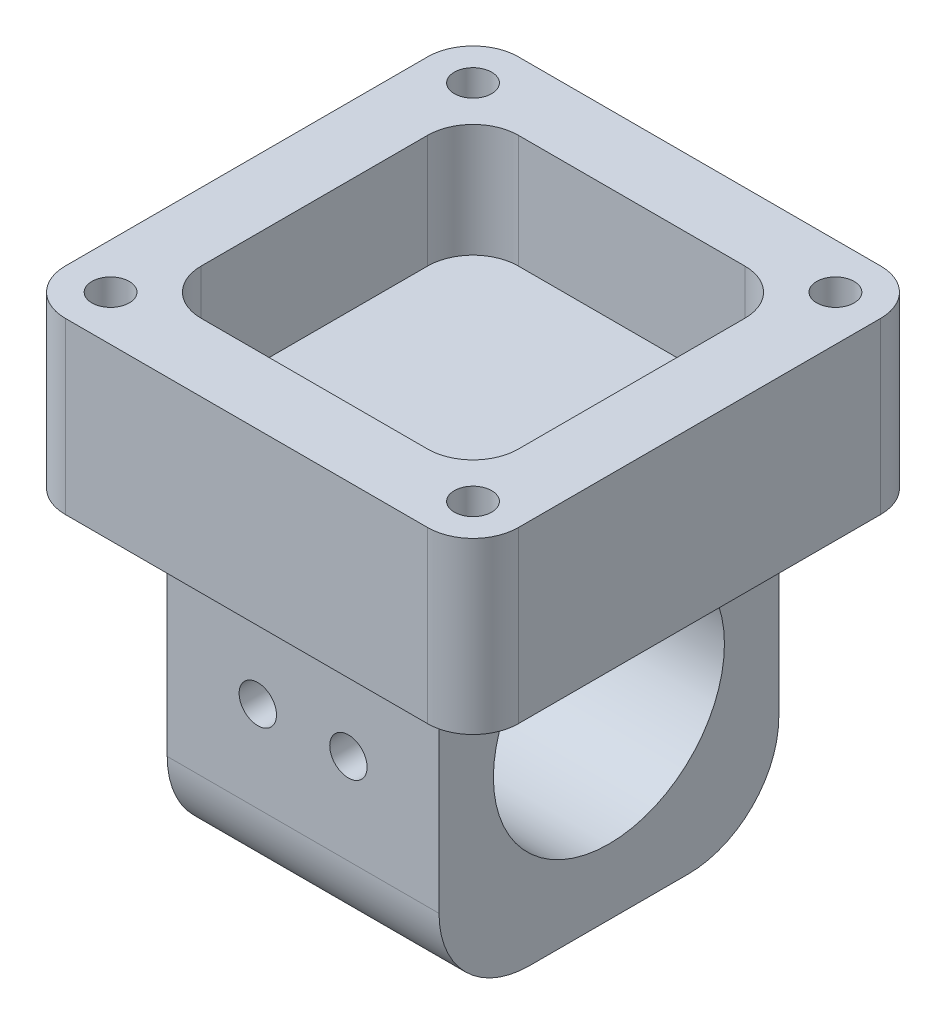
SolidWorks part; units mm, degrees
ref_plane "Front Plane" through (0, 0, 0) normal (0, 0, 1) x (1, 0, 0)
ref_plane "Top Plane" through (0, 0, 0) normal (0, 1, 0) x (1, 0, 0)
ref_plane "Right Plane" through (0, 0, 0) normal (1, 0, 0) x (0, 0, -1)
sketch "Sketch1" plane through (0, 0, 0) normal (0, 1, 0) x (1, 0, 0)
  line L1 (-12, -15) -> (12, -15)
  line L2 (-12, -15) -> (-12, 15)
  line L3 (-12, 15) -> (12, 15)
  line L4 (12, -15) -> (12, 15)
  line L5 (-12, -15) -> (12, 15) construction
  line L6 (-12, 15) -> (12, -15) construction
  point P0 (0, 0)
  dimension "D1" = 30
  dimension "D2" = 24
extrude "Boss-Extrude1" add sketch "Sketch1" along normal mid plane 22
sketch "Sketch2" plane through (0, 0, -15) normal (0, 0, -1) x (-1, 0, 0)
  line L0 (0, 0) -> (0, -5.5397) construction
  circle A0 centre (4, 0) radius 1.65
  circle A2 centre (-4, 0) radius 1.65
  dimension "D1" = 3.3
  dimension "D2" = 4
extrude "Cut-Extrude1" cut sketch "Sketch2" against normal up to surface (30 mm away) up to face at (0, 0, 15)
sketch "Sketch3" plane through (-12, 0, 0) normal (-1, 0, 0) x (0, 0, 1)
  circle A0 centre (0, 0) radius 10.2
  dimension "D1" = 20.4
extrude "Cut-Extrude2" cut sketch "Sketch3" against normal up to surface (24 mm away) up to face at (12, 0, 0)
ref_plane "Plane1" through (0, 16, 0) normal (0, 1, 0) x (1, 0, 0)
sketch "Sketch5" plane through (0, 16, 0) normal (0, 1, 0) x (1, 0, 0)
  line L1 (20, 20) -> (-20, 20)
  line L2 (20, 20) -> (20, -20)
  line L3 (20, -20) -> (-20, -20)
  line L4 (-20, 20) -> (-20, -20)
  line L5 (20, 20) -> (-20, -20) construction
  line L6 (20, -20) -> (-20, 20) construction
  point P0 (0, 0)
  dimension "D1" = 40
extrude "Boss-Extrude3" add sketch "Sketch5" against normal up to surface (5 mm away) up to face at (0, 11, 0)
sketch "Sketch8" plane through (0, 16, 0) normal (0, 1, 0) x (1, 0, 0)
  line L1 (20, 20) -> (-20, 20)
  line L2 (20, 20) -> (20, -20)
  line L3 (20, -20) -> (-20, -20)
  line L4 (-20, 20) -> (-20, -20)
  line L5 (20, 20) -> (-20, -20) construction
  line L6 (20, -20) -> (-20, 20) construction
  line L7 (14, 14) -> (-14, 14)
  line L8 (14, 14) -> (14, -14)
  line L9 (14, -14) -> (-14, -14)
  line L10 (-14, 14) -> (-14, -14)
  line L11 (14, 14) -> (-14, -14) construction
  line L12 (14, -14) -> (-14, 14) construction
  point P0 (0, 0)
  point P7 (0, 0)
  line M9 (-20, 20) -> (-20, -20)
  line M10 (-20, -20) -> (20, -20)
  line M11 (20, -20) -> (20, 20)
  line M12 (20, 20) -> (-20, 20)
  dimension "D1" = 6
extrude "Boss-Extrude4" add sketch "Sketch8" along normal blind 10 contours L10 L7 L8 L9 M12 M9 M10 M11
sketch "Sketch9" plane through (0, 26, 0) normal (0, 1, 0) x (1, 0, 0)
  line L0 (0, 0) -> (-8.5639, 0) construction
  line L1 (0, 0) -> (0, -7.4354) construction
  line L4 (-20, -20) -> (20, -20) construction
  line L5 (20, -20) -> (20, 20) construction
  circle A0 centre (-16, 16) radius 1.65
  circle A1 centre (16, 16) radius 1.65
  circle A2 centre (16, -16) radius 1.65
  circle A3 centre (-16, -16) radius 1.65
  dimension "D1" = 4
  dimension "D2" = 4
  dimension "D3" = 3.3
extrude "Cut-Extrude3" cut sketch "Sketch9" against normal up to surface (15 mm away) up to face at (0, 11, 0)
fillet "Fillet3" radius 4 8 edges at (14, 21, -14) (-14, 21, 14) (20, 18.5, 20) (-14, 21, -14) (-20, 18.5, 20) (20, 18.5, -20) (14, 21, 14) (-20, 18.5, -20)
sketch "Sketch10" plane through (0, -11, 0) normal (0, -1, 0) x (1, 0, 0)
  line L1 (-12, -15) -> (12, -15)
  line L2 (-12, -15) -> (-12, 15)
  line L3 (-12, 15) -> (12, 15)
  line L4 (12, -15) -> (12, 15)
  line L5 (-12, -15) -> (12, 15) construction
  line L6 (-12, 15) -> (12, -15) construction
  point P0 (0, 0)
extrude "Boss-Extrude5" add sketch "Sketch10" along normal blind 5
fillet "Fillet6" radius 8 2 edges at (0, -16, 15) (0, -16, -15)
